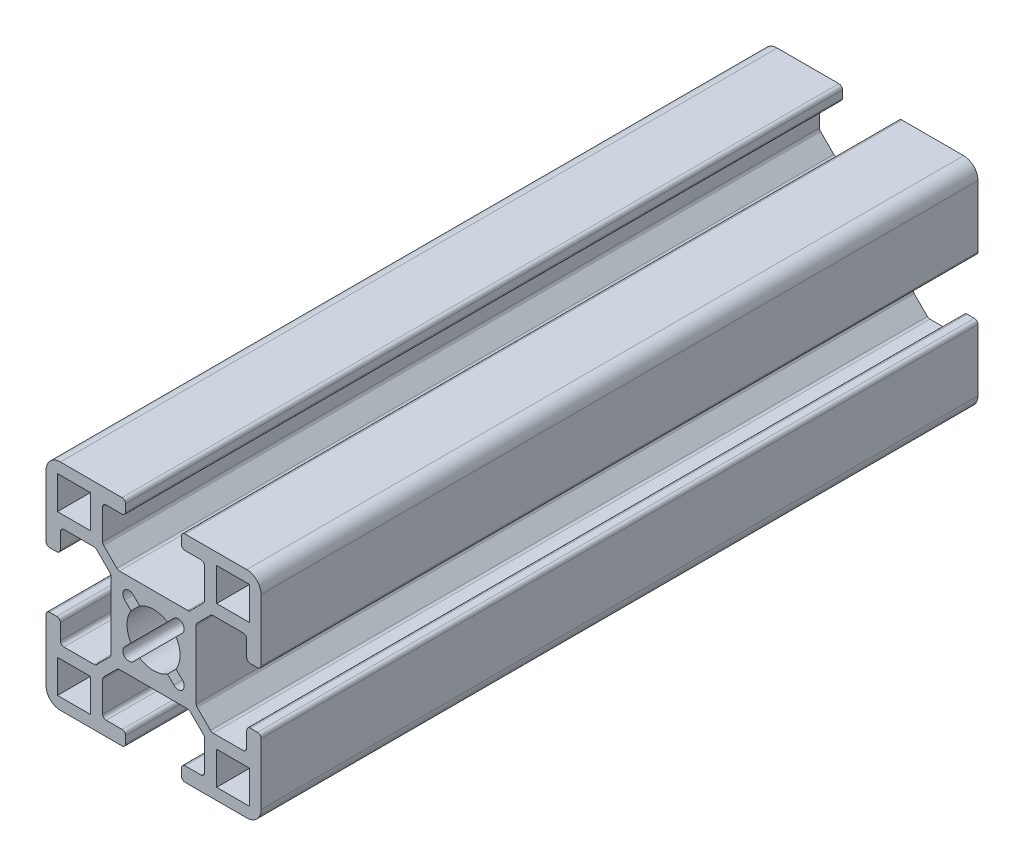
SolidWorks part; units mm, degrees
material "6063-T5"
ref_plane "Front Plane" through (0, 0, 0) normal (0, 0, 1) x (1, 0, 0)
ref_plane "Top Plane" through (0, 0, 0) normal (0, 1, 0) x (1, 0, 0)
ref_plane "Right Plane" through (0, 0, 0) normal (1, 0, 0) x (0, 0, -1)
sketch "Sketch1" plane through (0, 0, 0) normal (0, 0, 1) x (1, 0, 0)
  line L24 (-8.8, -8.8) -> (-13.4, -8.8)
  line L25 (-13.4, -8.8) -> (-13.4, -13.4)
  line L26 (-13.4, -13.4) -> (-8.8, -13.4)
  line L27 (-8.8, -13.4) -> (-8.8, -8.8)
  line L28 (8.8, -13.4) -> (13.4, -13.4)
  line L29 (13.4, -13.4) -> (13.4, -8.8)
  line L30 (8.8, -8.8) -> (8.8, -13.4)
  line L31 (13.4, -8.8) -> (8.8, -8.8)
  line L32 (13.4, 8.8) -> (13.4, 13.4)
  line L33 (13.4, 13.4) -> (8.8, 13.4)
  line L34 (8.8, 13.4) -> (8.8, 8.8)
  line L35 (8.8, 8.8) -> (13.4, 8.8)
  line L36 (4.0305, -2.8284) -> (3.1474, -1.9453)
  line L37 (1.9453, -3.1474) -> (2.8284, -4.0305)
  line L38 (-2.8284, -4.0305) -> (-1.9453, -3.1474)
  line L39 (-3.1474, -1.9453) -> (-4.0305, -2.8284)
  line L40 (-4.0305, 2.8284) -> (-3.1474, 1.9453)
  line L41 (3.1474, 1.9453) -> (4.0305, 2.8284)
  line L42 (2.8284, 4.0305) -> (1.9453, 3.1474)
  line L43 (-1.9453, 3.1474) -> (-2.8284, 4.0305)
  line L88 (15, -13) -> (15, -4.4)
  line L89 (14.5, -3.9) -> (13.5, -3.9)
  line L90 (13, -4.4) -> (13, -6.6)
  line L91 (12.5, -7.1) -> (8.2971, -7.1)
  line L92 (7.9435, -6.9536) -> (6.0964, -5.1065)
  line L93 (5.95, -4.7529) -> (5.95, 4.7529)
  line L94 (6.0964, 5.1065) -> (7.9435, 6.9536)
  line L95 (8.2971, 7.1) -> (12.5, 7.1)
  line L96 (13, 6.6) -> (13, 4.4)
  line L97 (13.5, 3.9) -> (14.5, 3.9)
  line L98 (15, 4.4) -> (15, 13)
  line L99 (13, 15) -> (4.4, 15)
  line L100 (3.9, 14.5) -> (3.9, 13.5)
  line L101 (4.4, 13) -> (6.6, 13)
  line L102 (7.1, 12.5) -> (7.1, 8.2971)
  line L103 (6.9536, 7.9435) -> (5.1065, 6.0964)
  line L104 (4.7529, 5.95) -> (-4.7529, 5.95)
  line L105 (-5.1065, 6.0964) -> (-6.9536, 7.9435)
  line L106 (-7.1, 8.2971) -> (-7.1, 12.5)
  line L107 (-6.6, 13) -> (-4.4, 13)
  line L108 (-3.9, 13.5) -> (-3.9, 14.5)
  line L109 (-4.4, 15) -> (-13, 15)
  line L110 (-15, 13) -> (-15, 4.4)
  line L111 (-14.5, 3.9) -> (-13.5, 3.9)
  line L112 (-13, 4.4) -> (-13, 6.6)
  line L113 (-12.5, 7.1) -> (-8.2971, 7.1)
  line L114 (-7.9435, 6.9536) -> (-6.0964, 5.1065)
  line L115 (-5.95, 4.7529) -> (-5.95, -4.7529)
  line L116 (-6.0964, -5.1065) -> (-7.9435, -6.9536)
  line L117 (-8.2971, -7.1) -> (-12.5, -7.1)
  line L118 (-13, -6.6) -> (-13, -4.4)
  line L119 (-13.5, -3.9) -> (-14.5, -3.9)
  line L120 (-15, -4.4) -> (-15, -13)
  line L121 (-13, -15) -> (-4.4, -15)
  line L122 (-3.9, -14.5) -> (-3.9, -13.5)
  line L123 (-4.4, -13) -> (-6.6, -13)
  line L124 (-7.1, -12.5) -> (-7.1, -8.2971)
  line L125 (-6.9536, -7.9435) -> (-5.1065, -6.0964)
  line L126 (-4.7529, -5.95) -> (4.7529, -5.95)
  line L127 (5.1065, -6.0964) -> (6.9536, -7.9435)
  line L128 (7.1, -8.2971) -> (7.1, -12.5)
  line L129 (6.6, -13) -> (4.4, -13)
  line L130 (3.9, -13.5) -> (3.9, -14.5)
  line L131 (4.4, -15) -> (13, -15)
  line L132 (-8.8, 8.8) -> (-8.8, 13.4)
  line L133 (-13.4, 8.8) -> (-8.8, 8.8)
  line L134 (-13.4, 13.4) -> (-13.4, 8.8)
  line L135 (-8.8, 13.4) -> (-13.4, 13.4)
  arc A8 (-4.0305, -2.8284) -> (-2.8284, -4.0305) centre (-3.4295, -3.4295) ccw
  arc A9 (2.8284, -4.0305) -> (4.0305, -2.8284) centre (3.4295, -3.4295) ccw
  arc A10 (-1.9453, -3.1474) -> (1.9453, -3.1474) centre (0, 0) ccw
  arc A11 (-3.1474, 1.9453) -> (-3.1474, -1.9453) centre (0, 0) ccw
  arc A12 (3.1474, -1.9453) -> (3.1474, 1.9453) centre (0, 0) ccw
  arc A13 (4.0305, 2.8284) -> (2.8284, 4.0305) centre (3.4295, 3.4295) ccw
  arc A14 (1.9453, 3.1474) -> (-1.9453, 3.1474) centre (0, 0) ccw
  arc A15 (-2.8284, 4.0305) -> (-4.0305, 2.8284) centre (-3.4295, 3.4295) ccw
  arc A88 (13, -15) -> (15, -13) centre (13, -13) ccw
  arc A89 (15, -4.4) -> (14.5, -3.9) centre (14.5, -4.4) ccw
  arc A90 (13.5, -3.9) -> (13, -4.4) centre (13.5, -4.4) ccw
  arc A91 (12.5, -7.1) -> (13, -6.6) centre (12.5, -6.6) ccw
  arc A92 (7.9435, -6.9536) -> (8.2971, -7.1) centre (8.2971, -6.6) ccw
  arc A93 (5.95, -4.7529) -> (6.0964, -5.1065) centre (6.45, -4.7529) ccw
  arc A94 (6.0964, 5.1065) -> (5.95, 4.7529) centre (6.45, 4.7529) ccw
  arc A95 (8.2971, 7.1) -> (7.9435, 6.9536) centre (8.2971, 6.6) ccw
  arc A96 (13, 6.6) -> (12.5, 7.1) centre (12.5, 6.6) ccw
  arc A97 (13, 4.4) -> (13.5, 3.9) centre (13.5, 4.4) ccw
  arc A98 (14.5, 3.9) -> (15, 4.4) centre (14.5, 4.4) ccw
  arc A99 (15, 13) -> (13, 15) centre (13, 13) ccw
  arc A100 (4.4, 15) -> (3.9, 14.5) centre (4.4, 14.5) ccw
  arc A101 (3.9, 13.5) -> (4.4, 13) centre (4.4, 13.5) ccw
  arc A102 (7.1, 12.5) -> (6.6, 13) centre (6.6, 12.5) ccw
  arc A103 (6.9536, 7.9435) -> (7.1, 8.2971) centre (6.6, 8.2971) ccw
  arc A104 (4.7529, 5.95) -> (5.1065, 6.0964) centre (4.7529, 6.45) ccw
  arc A105 (-5.1065, 6.0964) -> (-4.7529, 5.95) centre (-4.7529, 6.45) ccw
  arc A106 (-7.1, 8.2971) -> (-6.9536, 7.9435) centre (-6.6, 8.2971) ccw
  arc A107 (-6.6, 13) -> (-7.1, 12.5) centre (-6.6, 12.5) ccw
  arc A108 (-4.4, 13) -> (-3.9, 13.5) centre (-4.4, 13.5) ccw
  arc A109 (-3.9, 14.5) -> (-4.4, 15) centre (-4.4, 14.5) ccw
  arc A110 (-13, 15) -> (-15, 13) centre (-13, 13) ccw
  arc A111 (-15, 4.4) -> (-14.5, 3.9) centre (-14.5, 4.4) ccw
  arc A112 (-13.5, 3.9) -> (-13, 4.4) centre (-13.5, 4.4) ccw
  arc A113 (-12.5, 7.1) -> (-13, 6.6) centre (-12.5, 6.6) ccw
  arc A114 (-7.9435, 6.9536) -> (-8.2971, 7.1) centre (-8.2971, 6.6) ccw
  arc A115 (-5.95, 4.7529) -> (-6.0964, 5.1065) centre (-6.45, 4.7529) ccw
  arc A116 (-6.0964, -5.1065) -> (-5.95, -4.7529) centre (-6.45, -4.7529) ccw
  arc A117 (-8.2971, -7.1) -> (-7.9435, -6.9536) centre (-8.2971, -6.6) ccw
  arc A118 (-13, -6.6) -> (-12.5, -7.1) centre (-12.5, -6.6) ccw
  arc A119 (-13, -4.4) -> (-13.5, -3.9) centre (-13.5, -4.4) ccw
  arc A120 (-14.5, -3.9) -> (-15, -4.4) centre (-14.5, -4.4) ccw
  arc A121 (-15, -13) -> (-13, -15) centre (-13, -13) ccw
  arc A122 (-4.4, -15) -> (-3.9, -14.5) centre (-4.4, -14.5) ccw
  arc A123 (-3.9, -13.5) -> (-4.4, -13) centre (-4.4, -13.5) ccw
  arc A124 (-7.1, -12.5) -> (-6.6, -13) centre (-6.6, -12.5) ccw
  arc A125 (-6.9536, -7.9435) -> (-7.1, -8.2971) centre (-6.6, -8.2971) ccw
  arc A126 (-4.7529, -5.95) -> (-5.1065, -6.0964) centre (-4.7529, -6.45) ccw
  arc A127 (5.1065, -6.0964) -> (4.7529, -5.95) centre (4.7529, -6.45) ccw
  arc A128 (7.1, -8.2971) -> (6.9536, -7.9435) centre (6.6, -8.2971) ccw
  arc A129 (6.6, -13) -> (7.1, -12.5) centre (6.6, -12.5) ccw
  arc A130 (4.4, -13) -> (3.9, -13.5) centre (4.4, -13.5) ccw
  arc A131 (3.9, -14.5) -> (4.4, -15) centre (4.4, -14.5) ccw
  dimension "D1" = 30
  dimension "D2" = 30
extrude "Boss-Extrude1" add sketch "Sketch1" along normal mid plane 100
